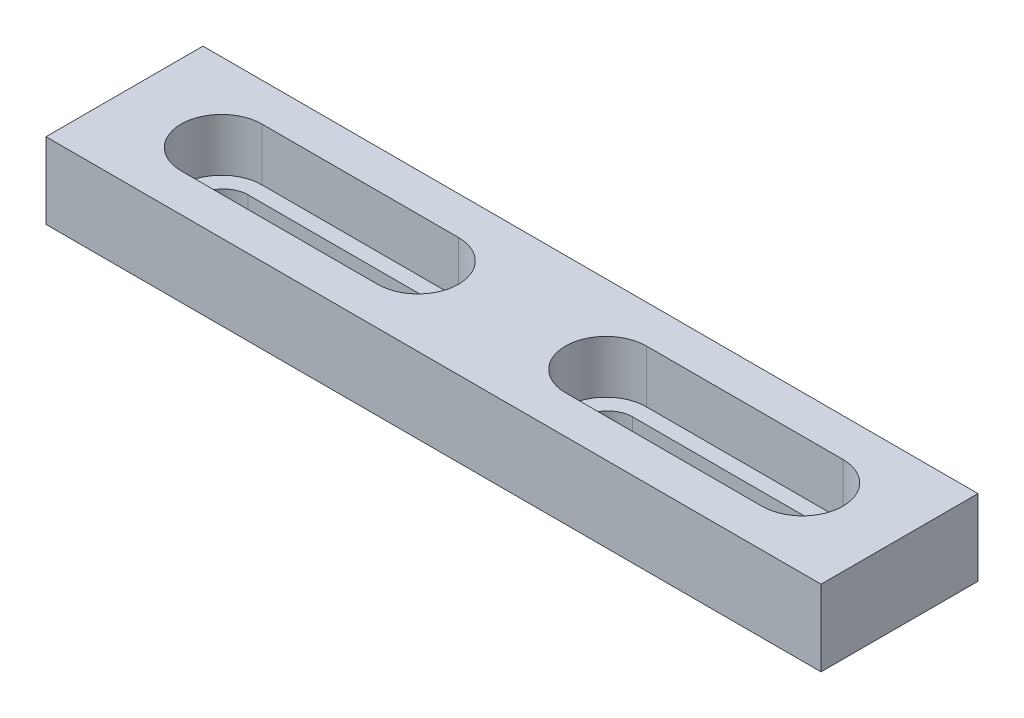
SolidWorks part; units mm, degrees
ref_plane "前视基准面" through (0, 0, 0) normal (0, 0, 1) x (1, 0, 0)
ref_plane "上视基准面" through (0, 0, 0) normal (0, 1, 0) x (1, 0, 0)
ref_plane "右视基准面" through (0, 0, 0) normal (1, 0, 0) x (0, 0, -1)
sketch "草图2" plane through (0, 0, 0) normal (0, 1, 0) x (1, 0, 0)
  line L1 (-50, -10.125) -> (50, -10.125)
  line L2 (-50, -10.125) -> (-50, 10.125)
  line L3 (-50, 10.125) -> (50, 10.125)
  line L4 (50, -10.125) -> (50, 10.125)
  point P0 (0, 0)
  dimension "D1" = 100
  dimension "D2" = 20.25
extrude "凸台-拉伸2" add sketch "草图2" along normal blind 9.8
sketch "草图6" plane through (0, 0, 0) normal (0, 1, 0) x (1, 0, 0)
  line L0 (-37.475, 0) -> (-12.125, 0) construction
  line L1 (-37.475, 5.225) -> (-12.125, 5.225)
  line L2 (-37.475, -5.225) -> (-12.125, -5.225)
  line L3 (-50, 0) -> (-24.8, 0)
  line L4 (-50, 10.125) -> (-50, -10.125) construction
  line L5 (0, 0) -> (0, 10.125)
  line L6 (50, 10.125) -> (-50, 10.125) construction
  line L7 (37.475, -5.225) -> (12.125, -5.225)
  line L8 (37.475, 5.225) -> (12.125, 5.225)
  arc A0 (-37.475, 5.225) -> (-37.475, -5.225) centre (-37.475, 0) ccw
  arc A1 (-12.125, -5.225) -> (-12.125, 5.225) centre (-12.125, 0) ccw
  arc A2 (37.475, 5.225) -> (37.475, -5.225) centre (37.475, 0) cw
  arc A3 (12.125, -5.225) -> (12.125, 5.225) centre (12.125, 0) cw
  point P7 (-42.7, 0)
  point P8 (-6.9, 0)
  point P18 (-24.8, 0)
  dimension "D1" = 35.8
extrude "切除-拉伸4" cut sketch "草图6" along normal blind 9.8
sketch "草图8" plane through (0, 0, 0) normal (0, -1, 0) x (1, 0, 0)
  line L0 (-50, 0) -> (-24.8, 0)
  line L1 (-50, -10.125) -> (-50, 10.125) construction
  line L2 (-37.25, 0) -> (-12.35, 0) construction
  line L3 (-37.25, 3.215) -> (-12.35, 3.215)
  line L4 (-37.25, -3.215) -> (-12.35, -3.215)
  line L5 (0, 0) -> (0, 10.125)
  line L6 (-50, 10.125) -> (50, 10.125) construction
  line L7 (37.25, -3.215) -> (12.35, -3.215)
  line L8 (37.25, 3.215) -> (12.35, 3.215)
  line L9 (-37.475, 0) -> (-12.125, 0) construction
  line L10 (-37.475, 5.225) -> (-12.125, 5.225)
  line L11 (-37.475, -5.225) -> (-12.125, -5.225)
  line L12 (37.475, 5.225) -> (12.125, 5.225)
  line L13 (37.475, -5.225) -> (12.125, -5.225)
  arc A0 (-37.25, 3.215) -> (-37.25, -3.215) centre (-37.25, 0) ccw
  arc A1 (-12.35, -3.215) -> (-12.35, 3.215) centre (-12.35, 0) ccw
  arc A2 (12.35, -3.215) -> (12.35, 3.215) centre (12.35, 0) cw
  arc A3 (37.25, 3.215) -> (37.25, -3.215) centre (37.25, 0) cw
  arc A4 (-37.475, 5.225) -> (-37.475, -5.225) centre (-37.475, 0) ccw
  arc A5 (-12.125, -5.225) -> (-12.125, 5.225) centre (-12.125, 0) ccw
  arc A6 (12.125, -5.225) -> (12.125, 5.225) centre (12.125, 0) cw
  arc A7 (37.475, 5.225) -> (37.475, -5.225) centre (37.475, 0) cw
  point P12 (-40.465, 0)
  point P13 (-9.135, 0)
  point P30 (-6.9, 0)
  point P31 (-42.7, 0)
  point P32 (-24.8, 0)
  dimension "D1" = 31.33
  dimension "D2" = 35.8
extrude "凸台-拉伸3" add sketch "草图8" against normal blind 3
